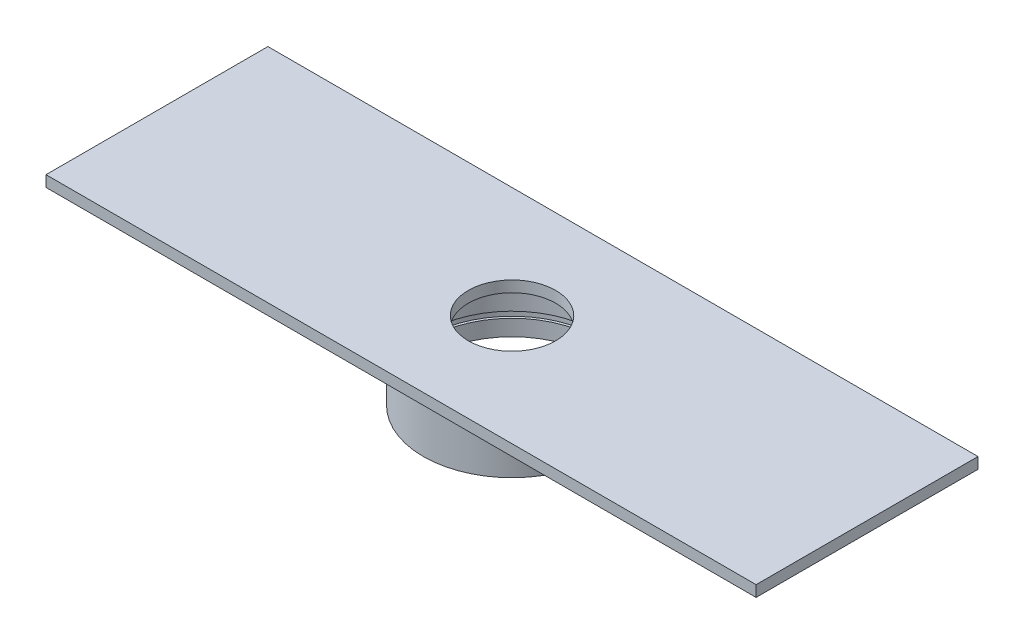
SolidWorks part; units mm, degrees
ref_plane "Front Plane" through (0, 0, 0) normal (0, 0, 1) x (1, 0, 0)
ref_plane "Top Plane" through (0, 0, 0) normal (0, 1, 0) x (1, 0, 0)
ref_plane "Right Plane" through (0, 0, 0) normal (1, 0, 0) x (0, 0, -1)
sketch "Sketch1" plane through (0, 0, 0) normal (0, 1, 0) x (1, 0, 0)
  circle A0 centre (0, 0) radius 24
  circle A1 centre (0, 0) radius 25.4
  point P0 (0, 0)
extrude "Boss-Extrude1" add sketch "Sketch1" along normal blind 19.05
ref_plane "Plane1" through (0, 6.35, 0) normal (0, -1, 0) x (-1, 0, 0)
sketch "Sketch3" plane through (0, 6.35, 0) normal (0, -1, 0) x (-1, 0, 0)
  circle A0 centre (0, 0) radius 24.7
extrude "Cut-Extrude1" cut sketch "Sketch3" along normal blind 1.75
sketch "Sketch4" plane through (0, 19.05, 0) normal (0, 1, 0) x (1, 0, 0)
  line L0 (-101.6, 31.75) -> (-101.6, -31.75)
  line L1 (-101.6, -31.75) -> (101.6, -31.75)
  line L2 (101.6, -31.75) -> (101.6, 31.75)
  line L3 (101.6, 31.75) -> (-101.6, 31.75)
  circle A0 centre (0, 0) radius 12.5
  point P0 (-101.6, 31.75)
  point P1 (101.6, -31.75)
  point P2 (-101.6, -31.75)
  point P3 (101.6, 31.75)
extrude "Boss-Extrude2" add sketch "Sketch4" along normal blind 3.175
